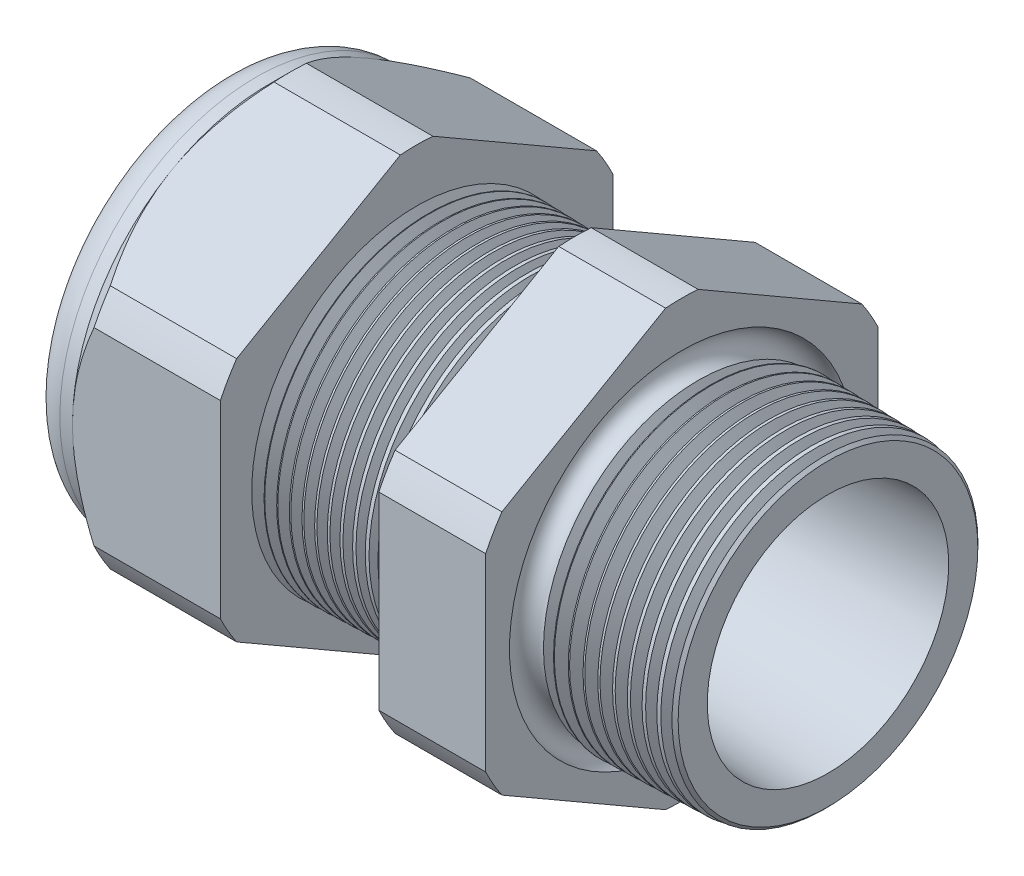
SolidWorks part; units mm, degrees
ref_plane "Front Plane" through (0, 0, 0) normal (0, 0, 1) x (1, 0, 0)
ref_plane "Top Plane" through (0, 0, 0) normal (0, 1, 0) x (1, 0, 0)
ref_plane "Right Plane" through (0, 0, 0) normal (1, 0, 0) x (0, 0, -1)
sketch "Sketch10" plane through (0, 0, 0) normal (0, 0, 1) x (1, 0, 0)
  line L0 (0, 0) -> (-115.3565, 0) construction
  line L1 (-35.814, 5.969) -> (-24.014, 5.969)
  line L2 (1.016, 7.3456) -> (1.016, 9.3776)
  line L3 (-7.874, 9.6104) -> (1.016, 9.3776)
  line L4 (-7.874, 23.876) -> (-7.874, 9.6104)
  line L5 (-7.874, 23.876) -> (-14.374, 23.876)
  line L6 (-14.374, 23.876) -> (-14.374, 9.7806)
  line L7 (-24.014, 10.033) -> (-14.374, 9.7806)
  line L8 (-24.014, 10.033) -> (-24.014, 23.876)
  line L9 (-24.014, 23.876) -> (-33.014, 23.876)
  line L10 (-33.014, 23.876) -> (-33.014, 11.938)
  line L11 (-33.014, 11.938) -> (-35.814, 11.938)
  line L12 (-35.814, 11.938) -> (-35.814, 5.969)
  line L13 (-24.014, 5.969) -> (1.016, 7.3456)
  dimension "D1" = 36.83
  dimension "D2" = 11.938
  dimension "D3" = 1.5
  dimension "D4" = 2.032
  dimension "A" = 20.066
  dimension "D6" = 23.876
  dimension "D8" = 47.752
  dimension "D9" = 2.8
  dimension "D10" = 9
  dimension "D11" = 6.5
  dimension "D" = 8.89
revolve "Revolve2" add sketch "Sketch10" angle 360 about L0
sketch "Sketch12" plane through (-33.014, 0, 0) normal (-1, 0, 0) x (0, 0, 1)
  line L1 (-0.9882, 13.2143) -> (-10.9498, 7.4629)
  line L2 (-11.938, 5.7513) -> (-11.938, -5.7513)
  line L3 (-10.9498, -7.4629) -> (-0.9882, -13.2143)
  line L4 (0.9882, -13.2143) -> (10.9498, -7.4629)
  line L5 (11.938, -5.7513) -> (11.938, 5.7513)
  line L6 (10.9498, 7.4629) -> (0.9882, 13.2143)
  circle A0 centre (0, 0) radius 11.938 construction
  arc A1 (0.9882, 13.2143) -> (-0.9882, 13.2143) centre (0, 0) ccw
  arc A2 (-10.9498, 7.4629) -> (-11.938, 5.7513) centre (0, 0) ccw
  arc A3 (-11.938, -5.7513) -> (-10.9498, -7.4629) centre (0, 0) ccw
  arc A4 (-0.9882, -13.2143) -> (0.9882, -13.2143) centre (0, 0) ccw
  arc A5 (10.9498, -7.4629) -> (11.938, -5.7513) centre (0, 0) ccw
  arc A6 (11.938, 5.7513) -> (10.9498, 7.4629) centre (0, 0) ccw
  dimension "D2" = 26.5024
  dimension "D1" = 23.876
extrude "Cut-Extrude2" cut sketch "Sketch12" against normal through all flip side to cut
fillet "Fillet4" radius 2.032 1 edges at (-35.814, 0, -11.938)
sketch "Sketch19" plane through (-33.014, 0, 0) normal (-1, 0, 0) x (0, 0, 1)
  line L0 (11.938, 0) -> (11.938, 5.7513) construction
  circle A0 centre (0, 0) radius 11.938
extrude "Cut-Extrude3" cut sketch "Sketch19" against normal blind 2 draft 45 flip side to cut
chamfer "Chamfer1" distance 0.254 angle 45 1 edges at (1.016, 0, -9.3776)
sketch "Sketch21" plane through (-35.814, 0, 0) normal (-1, 0, 0) x (0, 0, 1)
  circle A0 centre (0, 0) radius 5.969
  circle A2 centre (0, 0) radius 5.969 construction
extrude "plug" add sketch "Sketch21" against normal blind 6.35 separate body
sketch "Sketch22" plane through (-35.814, 0, 0) normal (-1, 0, 0) x (0, 0, 1)
  circle A0 centre (0, 0) radius 5.715
  circle A1 centre (0, 0) radius 5.969 construction
  dimension "D1" = 0.254
extrude "Cut-Extrude4" cut sketch "Sketch22" against normal blind 0.508
sketch "Sketch27" plane through (-35.306, 0, 0) normal (-1, 0, 0) x (0, 0, 1)
  line L0 (-4.3624, 0) -> (4.3624, 0) construction
  circle A0 centre (-4.1849, 0) radius 1.524
  circle A1 centre (0, 0) radius 5.715 construction
  dimension "D1" = 0.0061
  dimension "holedia" = 3.048
extrude "plugholes" cut sketch "Sketch27" against normal through all
pattern_circular "CirPattern1" count 6 over 360 about axis through (0, 0, 0) along (1, 0, 0) of "plugholes"
sketch "Sketch28" [suppressed] plane through (-29.464, 0, 0) normal (-1, 0, 0) x (0, 0, 1)
  circle A0 centre (0, 0) radius 0.762
  dimension "midholedia" = 3.048
extrude "midhole" [suppressed] cut sketch "Sketch28" against normal through all
sketch "Sketch29" plane through (0, 0, 0) normal (0, 0, 1) x (1, 0, 0)
  line L0 (-24.014, 10.033) -> (-23.281, 10.0138)
  line L1 (-14.374, 9.7806) -> (-24.014, 10.033) construction
  line L2 (-23.281, 10.0138) -> (-23.6641, 9.3886)
  line L3 (-23.6641, 9.3886) -> (-24.014, 10.033)
  dimension "D1" = 60
  dimension "D2" = 60
  dimension "D3" = 0.635
revolve "Cut-Revolve1" cut sketch "Sketch29" angle 360 about axis through (0, 0, 0) along (-1, 0, 0)
pattern_linear "LPattern1" count 13 spacing 0.762 along (1, 0, 0) of "Cut-Revolve1"
sketch "Sketch30" plane through (0, 0, 0) normal (0, 0, 1) x (1, 0, 0)
  line L0 (-7.874, 9.6104) -> (-6.9944, 9.5873)
  line L1 (-7.874, 13.2143) -> (-7.874, 7.4629) construction
  line L2 (0.7621, 9.3842) -> (-7.874, 9.6104) construction
  line L3 (-6.9944, 9.5873) -> (-7.4542, 8.8371)
  line L4 (-7.4542, 8.8371) -> (-7.874, 9.6104)
  dimension "D1" = 60
  dimension "D2" = 60
  dimension "D3" = 0.762
revolve "Cut-Revolve2" cut sketch "Sketch30" angle 360 about axis through (0, 0, 0) along (-1, 0, 0)
pattern_linear "LPattern2" count 10 spacing 0.889 along (1, 0, 0) of "Cut-Revolve2"
sketch "Sketch31" [suppressed] plane through (-38.354, 0, 0) normal (-1, 0, 0) x (0, 0, 1)
  line L0 (-1.905, 1.905) -> (1.905, 1.905)
  line L1 (-1.905, -1.905) -> (1.905, -1.905)
  circle A0 centre (0, 0) radius 1.905 construction
  arc A1 (-1.905, 1.905) -> (-1.905, -1.905) centre (-1.905, 0) ccw
  arc A2 (1.905, 1.905) -> (1.905, -1.905) centre (1.905, 0) cw
extrude "Cut-Extrude5" [suppressed] cut sketch "Sketch31" against normal through all
sketch "Sketch32" plane through (0, 0, 0) normal (0, 0, 1) x (1, 0, 0)
  line L0 (-7.874, 13.2143) -> (-7.874, 7.4629) construction
  circle A0 centre (-7.747, 9.6104) radius 0.889
  dimension "D2" = 1.778
  dimension "D1" = 0.127
revolve "Cut-Revolve3" cut sketch "Sketch32" angle 360 about axis through (0, 0, 0) along (-1, 0, 0)
